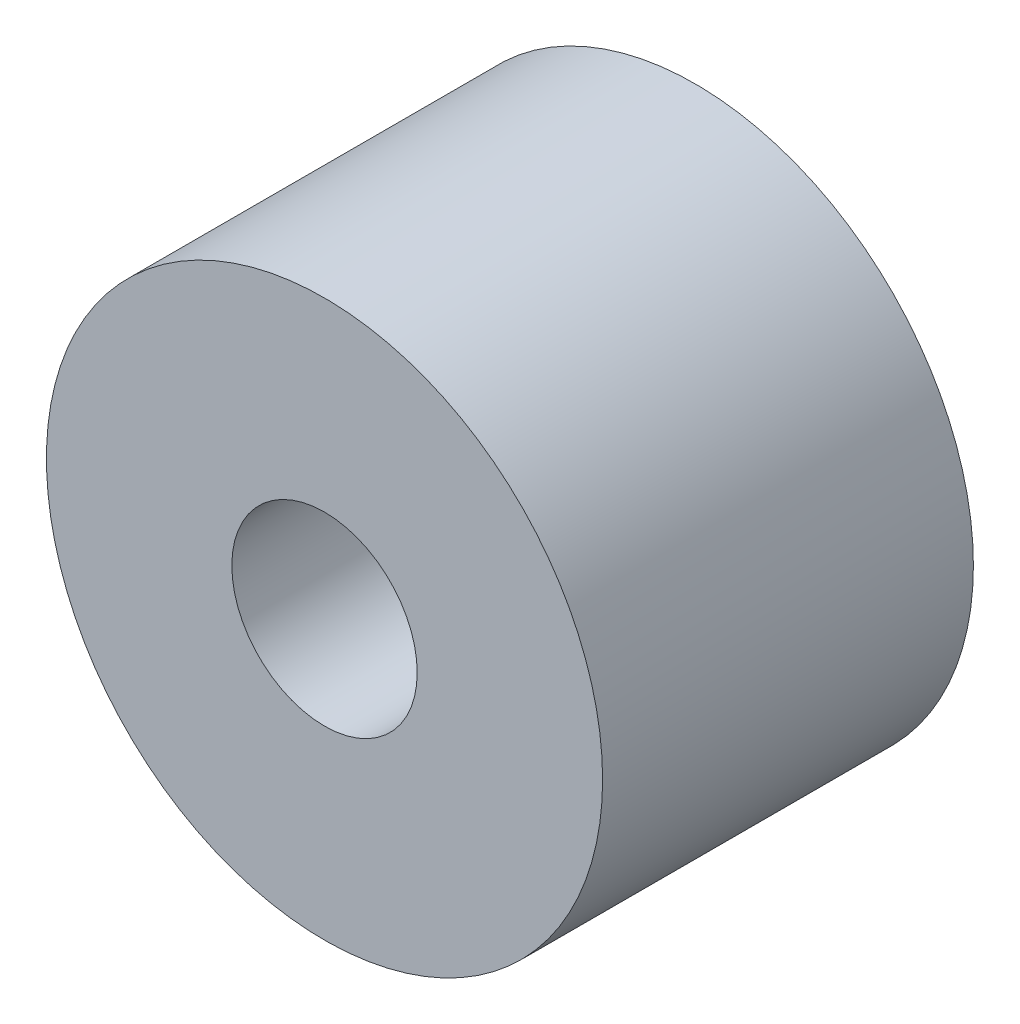
SolidWorks part; units mm, degrees
material "PA Type 6"
ref_plane "Front Plane" through (0, 0, 0) normal (0, 0, 1) x (1, 0, 0)
ref_plane "Top Plane" through (0, 0, 0) normal (0, 1, 0) x (1, 0, 0)
ref_plane "Right Plane" through (0, 0, 0) normal (1, 0, 0) x (0, 0, -1)
sketch "Sketch1" plane through (0, 0, 0) normal (0, 0, 1) x (1, 0, 0)
  circle A0 centre (0, 0) radius 2
  circle A1 centre (0, 0) radius 6
  dimension "D1" = 4
  dimension "D2" = 12
extrude "Boss-Extrude1" add sketch "Sketch1" along normal blind 8
